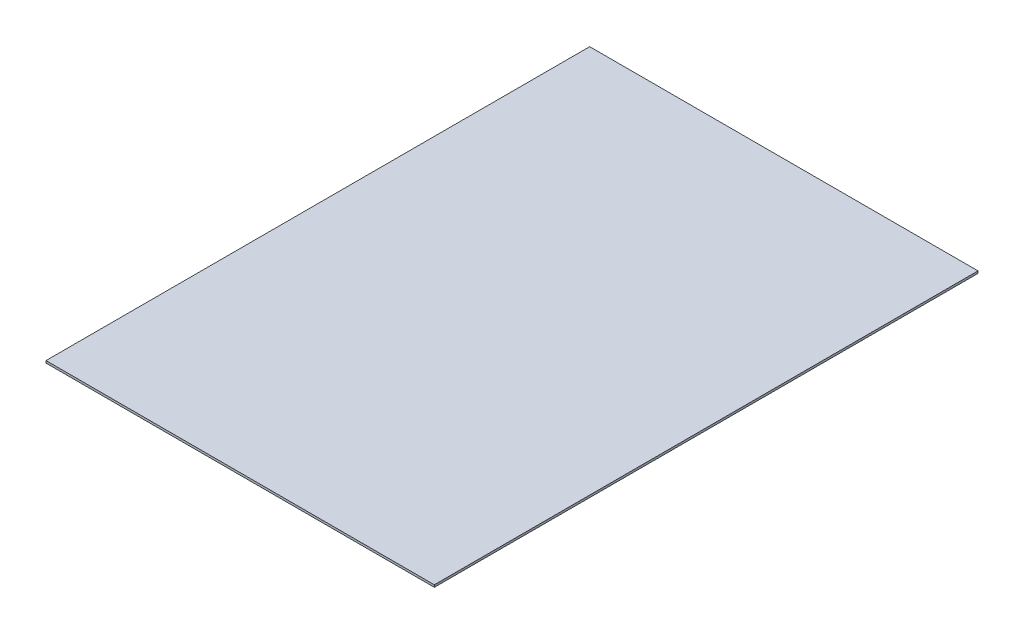
SolidWorks part; units mm, degrees
ref_plane "Спереди" through (0, 0, 0) normal (0, 0, 1) x (1, 0, 0)
ref_plane "Сверху" through (0, 0, 0) normal (0, 1, 0) x (1, 0, 0)
ref_plane "Справа" through (0, 0, 0) normal (1, 0, 0) x (0, 0, -1)
sketch "Эскиз1" plane through (0, 0, 0) normal (0, 1, 0) x (1, 0, 0)
  line L1 (-87.5, 122.5) -> (87.5, 122.5)
  line L2 (-87.5, 122.5) -> (-87.5, -122.5)
  line L3 (-87.5, -122.5) -> (87.5, -122.5)
  line L4 (87.5, 122.5) -> (87.5, -122.5)
  line L5 (-87.5, 122.5) -> (87.5, -122.5) construction
  line L6 (-87.5, -122.5) -> (87.5, 122.5) construction
  point P0 (0, 0)
extrude "Бобышка-Вытянуть1" add sketch "Эскиз1" along normal blind 1
